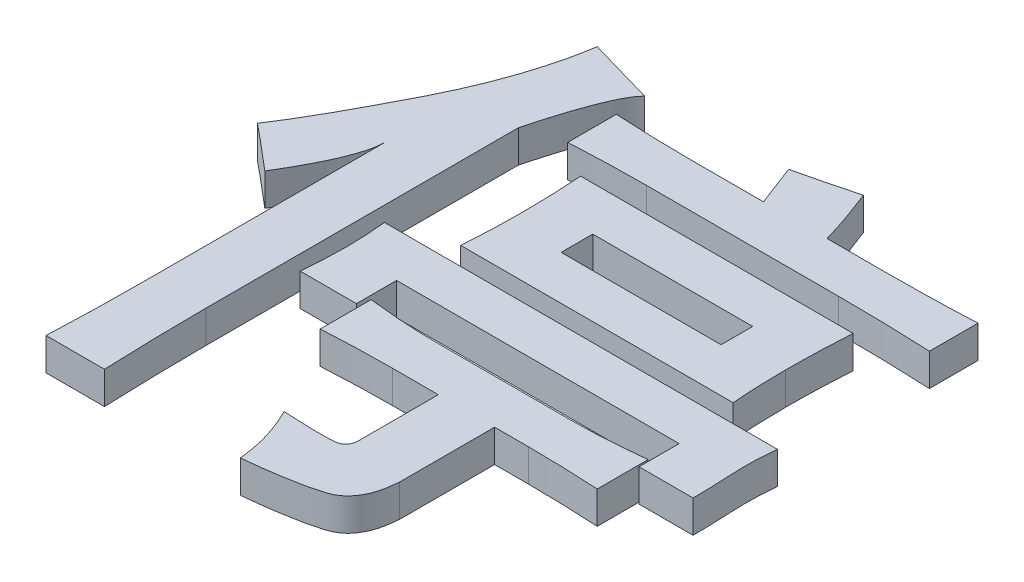
SolidWorks part; units mm, degrees
ref_plane "前视基准面" through (0, 0, 0) normal (0, 0, 1) x (1, 0, 0)
ref_plane "上视基准面" through (0, 0, 0) normal (0, 1, 0) x (1, 0, 0)
ref_plane "右视基准面" through (0, 0, 0) normal (1, 0, 0) x (0, 0, -1)
other "Configuration Table"
sketch "草图1" plane through (0, 0, 0) normal (0, 1, 0) x (1, 0, 0)
  text T0 "<b>停</b>" font "黑体" height 24
extrude "凸台-拉伸1" add sketch "草图1" along normal blind 2
